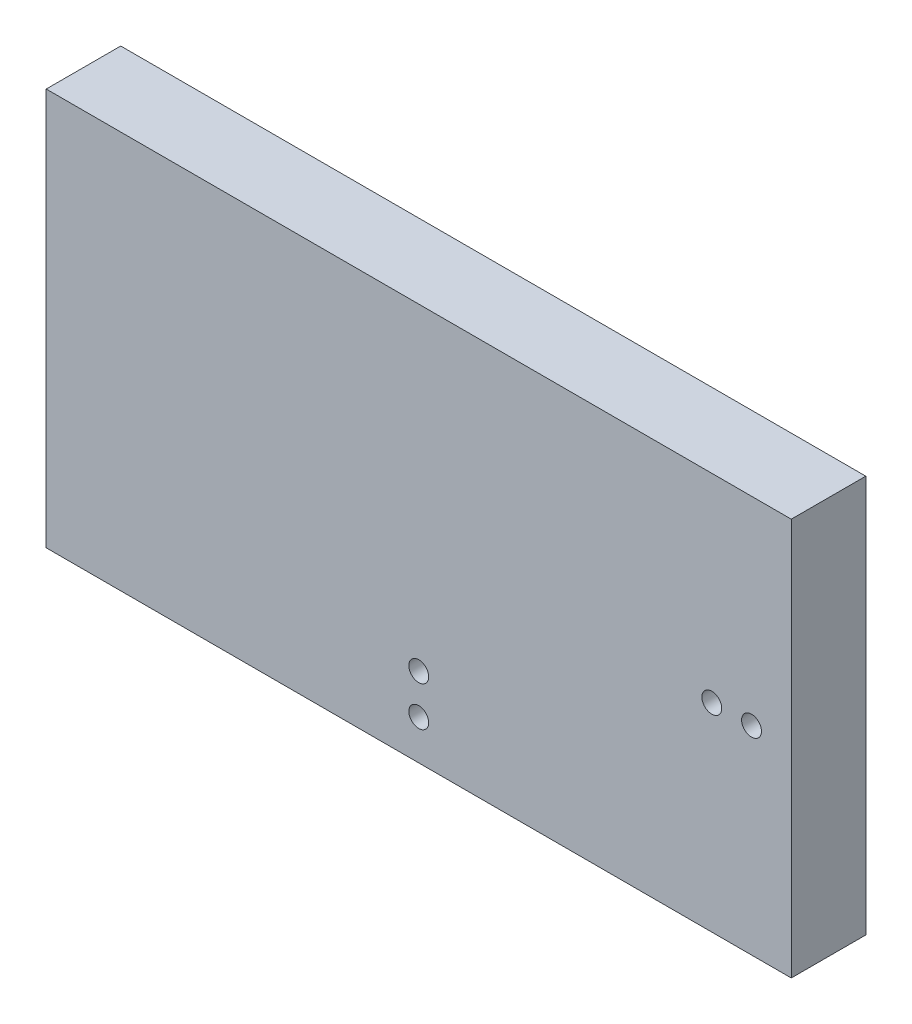
SolidWorks part; units mm, degrees
ref_plane "Plan de face" through (0, 0, 0) normal (0, 0, 1) x (1, 0, 0)
ref_plane "Plan de dessus" through (0, 0, 0) normal (0, 1, 0) x (1, 0, 0)
ref_plane "Plan de droite" through (0, 0, 0) normal (1, 0, 0) x (0, 0, -1)
sketch "Esquisse2" plane through (0, 0, 0) normal (0, 0, 1) x (1, 0, 0)
  line L1 (-88.7337, 54.7226) -> (61.2663, 54.7226)
  line L2 (-88.7337, 54.7226) -> (-88.7337, -25.2774)
  line L3 (-88.7337, -25.2774) -> (61.2663, -25.2774)
  line L4 (61.2663, 54.7226) -> (61.2663, -25.2774)
  dimension "D1" = 150
  dimension "D2" = 80
extrude "Extrusion1" add sketch "Esquisse2" against normal blind 15
sketch "Esquisse3" plane through (0, 0, 0) normal (0, 0, 1) x (1, 0, 0)
  line L0 (-88.7337, 54.7226) -> (-88.7337, -25.2774) construction
  line L1 (-88.7337, -25.2774) -> (61.2663, -25.2774) construction
  line L2 (61.2663, -25.2774) -> (61.2663, 54.7226) construction
  circle A0 centre (-13.7337, -17.2774) radius 1.9976
  circle A1 centre (-13.7337, -9.2774) radius 2
  circle A2 centre (53.2663, 14.7226) radius 2
  circle A3 centre (45.2663, 14.7226) radius 2
  dimension "D3" = 4
  dimension "D5" = 4
  dimension "D9" = 4
  dimension "D1" = 75
  dimension "D2" = 8
  dimension "D4" = 8
  dimension "D6" = 8
  dimension "D7" = 40
  dimension "D8" = 8
extrude "Extrusion2" cut sketch "Esquisse3" against normal blind 10
